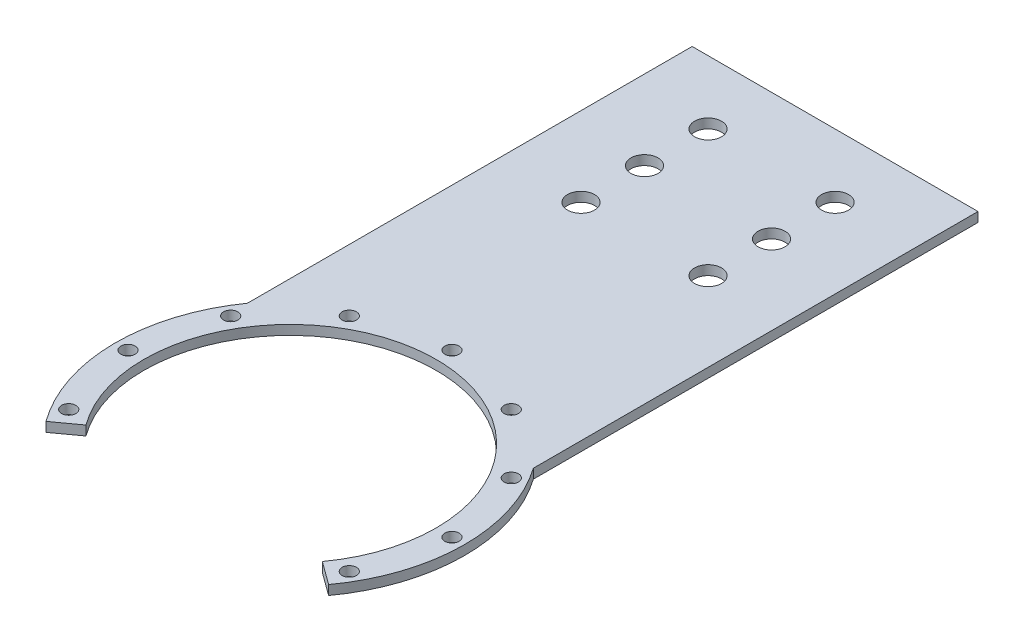
SolidWorks part; units mm, degrees
ref_plane "Front Plane" through (0, 0, 0) normal (0, 0, 1) x (1, 0, 0)
ref_plane "Top Plane" through (0, 0, 0) normal (0, 1, 0) x (1, 0, 0)
ref_plane "Right Plane" through (0, 0, 0) normal (1, 0, 0) x (0, 0, -1)
sketch "Sketch1" plane through (0, 0, 0) normal (0, 1, 0) x (1, 0, 0)
  circle A0 centre (0, 0) radius 55
  dimension "D1" = 110
extrude "Boss-Extrude1" add sketch "Sketch1" along normal blind 3
sketch "Sketch2" plane through (0, 0, 0) normal (0, 1, 0) x (1, 0, 0)
  line L0 (0, 0) -> (0, 101.6228) construction
  line L1 (-45, 171.6228) -> (-45, 31.6228)
  line L2 (-45, 171.6228) -> (45, 171.6228)
  line L3 (-45, 31.6228) -> (45, 31.6228)
  line L4 (45, 171.6228) -> (45, 31.6228)
  line L5 (0, 31.6228) -> (0, 171.6228) construction
  line L6 (-45, 101.6228) -> (45, 101.6228) construction
  circle A0 centre (0, 0) radius 55 construction
  dimension "D1" = 140
  dimension "D2" = 90
extrude "Boss-Extrude2" add sketch "Sketch2" along normal blind 3
sketch "Sketch4" plane through (0, 3, 0) normal (0, 1, 0) x (1, 0, 0)
  circle A0 centre (0, 0) radius 51 construction
  circle A1 centre (0, 0) radius 46
  dimension "D1" = 102
  dimension "D2" = 92
extrude "Cut-Extrude2" cut sketch "Sketch4" against normal through all both and the other way through all
sketch "Sketch7" plane through (0, 3, 0) normal (0, 1, 0) x (1, 0, 0)
  line L0 (0, 0) -> (0, -55)
  line L1 (0, 0) -> (-44.4959, -32.3282)
  arc A0 (-45, 31.6228) -> (45, 31.6228) centre (0, 0) ccw construction
  arc A1 (0, -55) -> (-44.4959, -32.3282) centre (0, 0) cw
  dimension "D1" = 54
extrude "Cut-Extrude5" cut sketch "Sketch7" against normal through all both and the other way through all
mirror "Mirror1" about plane through (0, 0, 0) normal (1, 0, 0) of "Cut-Extrude5"
sketch "Sketch5" plane through (0, 3, 0) normal (0, 1, 0) x (1, 0, 0)
  circle A0 centre (0, 0) radius 51 construction
  circle A1 centre (0, 51) radius 2.25
  dimension "D1" = 102
  dimension "D2" = 4.5
extrude "Cut-Extrude3" cut sketch "Sketch5" against normal through all both and the other way through all
pattern_circular "CirPattern1" count 12 over 360 about axis through (0, 0, 0) along (0, 1, 0) of "Cut-Extrude3"
sketch "Sketch6" plane through (0, 3, 0) normal (0, 1, 0) x (1, 0, 0)
  line L0 (0, 171.6228) -> (0, 0) construction
  line L1 (45, 171.6228) -> (-45, 171.6228) construction
  line L2 (-20, 151.6228) -> (20, 151.6228) construction
  circle A0 centre (20, 151.6228) radius 4.25
  circle A1 centre (-20, 151.6228) radius 4.25
  point P8 (0, 151.6228)
  dimension "D1" = 8.5
  dimension "D2" = 40
  dimension "D3" = 20
extrude "Cut-Extrude4" cut sketch "Sketch6" against normal through all both and the other way through all
pattern_linear "LPattern1" count 3 spacing 20 along (0, 0, 1) of "Cut-Extrude4"
